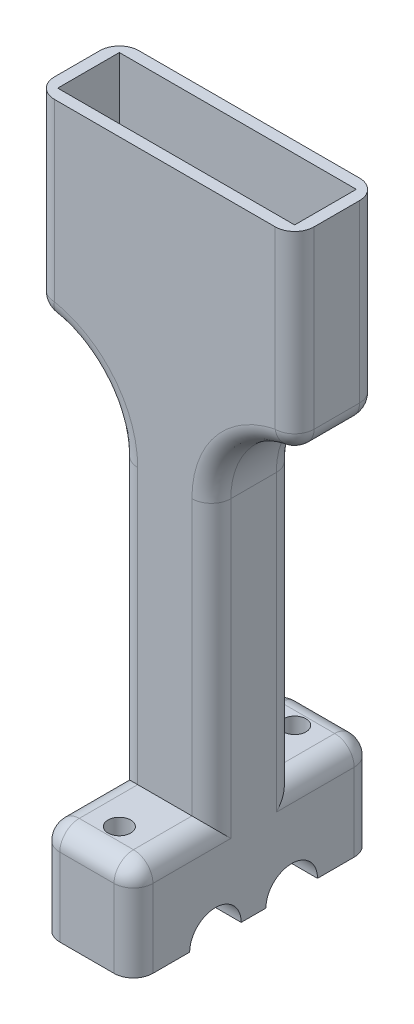
SolidWorks part; units mm, degrees
material "ABS"
ref_plane "Plano frontal" through (0, 0, 0) normal (0, 0, 1) x (1, 0, 0)
ref_plane "Plano superior" through (0, 0, 0) normal (0, 1, 0) x (1, 0, 0)
ref_plane "Plano direito" through (0, 0, 0) normal (1, 0, 0) x (0, 0, -1)
sketch "Esboço2" plane through (0, 0, 0) normal (0, 0, 1) x (1, 0, 0)
  line L0 (0, 50) -> (0, -50) construction
  line L1 (-20, 50) -> (20, 50)
  line L2 (-20, 50) -> (-20, 20)
  line L3 (20, 50) -> (20, 20)
  line L10 (-7.174, -50) -> (-7.174, 20)
  line L11 (-7.174, 20) -> (-20, 20)
  line L12 (7.174, -50) -> (7.174, 20)
  line L13 (7.174, 20) -> (20, 20)
  line L16 (-7.174, -50) -> (7.174, -50)
extrude "Ressalto-extrusão1" add sketch "Esboço2" along normal mid plane 13
fillet "Filete1" radius 3 1 edges at (-20, 20, 0)
fillet "Filete2" radius 3 1 edges at (20, 20, 0)
fillet "Filete3" radius 13 2 edges at (-7.174, 20, 0) (7.174, 20, 0)
sketch "Esboço4" plane through (0, 50, 0) normal (0, 1, 0) x (1, 0, 0)
  line L12 (-18.25, -4.75) -> (18.25, -4.75)
  line L13 (18.25, -4.75) -> (18.25, 4.75)
  line L14 (18.25, 4.75) -> (-18.25, 4.75)
  line L15 (-18.25, 4.75) -> (-18.25, -4.75)
  line L16 (-18.25, -4.75) -> (18.25, -4.75)
  line L17 (18.25, -4.75) -> (18.25, 4.75)
  line L18 (18.25, 4.75) -> (-18.25, 4.75)
  line L19 (-18.25, 4.75) -> (-18.25, -4.75)
  dimension "D1" = 1.75
extrude "Corte-extrusão1" cut sketch "Esboço4" against normal blind 25
sketch "Esboço11" plane through (0, 0, 6.5) normal (0, 0, 1) x (1, 0, 0)
  line L0 (-7.174, 7.318) -> (-7.174, -50) construction
  line L1 (7.174, -50) -> (-7.174, -50)
  line L2 (7.174, -50) -> (7.174, -35)
  line L3 (7.174, -35) -> (-7.174, -35)
  line L4 (-7.174, -50) -> (-7.174, -35)
extrude "Ressalto-extrusão5" add sketch "Esboço11" along normal blind 12
sketch "Esboço17" plane through (0, 0, -6.5) normal (0, 0, -1) x (-1, 0, 0)
  line L0 (7.174, 7.318) -> (7.174, -50) construction
  line L1 (-7.174, -50) -> (7.174, -50)
  line L2 (-7.174, -50) -> (-7.174, -35)
  line L3 (-7.174, -35) -> (7.174, -35)
  line L4 (7.174, -50) -> (7.174, -35)
extrude "Ressalto-extrusão6" add sketch "Esboço17" along normal blind 12
sketch "Esboço18" plane through (0, -50, 0) normal (0, -1, 0) x (1, 0, 0)
  line L0 (0, 18.5) -> (0, 13.5) construction
  line L1 (-7.174, 18.5) -> (7.174, 18.5) construction
  line L2 (0, 13.5) -> (0, -13.5) construction
  line L3 (0, -13.5) -> (0, -18.5) construction
  line L4 (7.174, -18.5) -> (-7.174, -18.5) construction
  circle A0 centre (0, 13.5) radius 1.75
  circle A1 centre (0, -13.5) radius 1.75
extrude "Corte-extrusão5" cut sketch "Esboço18" against normal blind 25
sketch "Esboço19" plane through (-7.174, 0, 0) normal (-1, 0, 0) x (0, 0, 1)
  line L0 (-18.5, -50) -> (-5.875, -50) construction
  line L1 (18.5, -50) -> (-18.5, -50) construction
  line L2 (-5.875, -50) -> (5.875, -50) construction
  line L3 (5.875, -50) -> (18.5, -50) construction
  circle A0 centre (-5.875, -50) radius 3.9688
  circle A1 centre (5.875, -50) radius 3.9688
extrude "Corte-extrusão6" cut sketch "Esboço19" against normal blind 25
fillet "Filete14" radius 3 26 edges at (20, 36.5, 6.5) (-20, 36.5, 6.5) (20, 36.5, -6.5) (-20, 36.5, -6.5) (-7.174, -42.5, 18.5) (-7.174, -35, 12.5) (0, -35, -18.5) (-7.174, -35, -12.5) (-7.174, -42.5, -18.5) (7.174, -42.5, -18.5) (7.174, -35, -12.5) (7.174, -42.5, 18.5) (7.174, -35, 12.5) (0, -35, 18.5)
